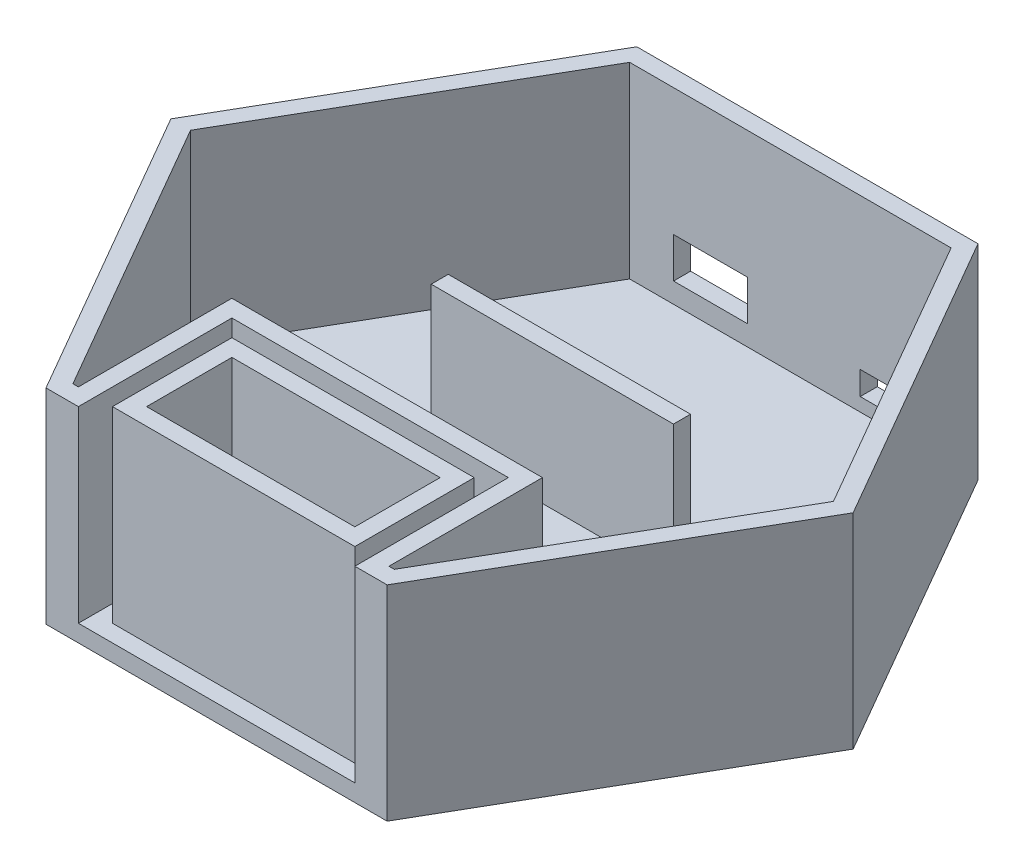
SolidWorks part; units mm, degrees
ref_plane "Front Plane" through (0, 0, 0) normal (0, 0, 1) x (1, 0, 0)
ref_plane "Top Plane" through (0, 0, 0) normal (0, 1, 0) x (1, 0, 0)
ref_plane "Right Plane" through (0, 0, 0) normal (1, 0, 0) x (0, 0, -1)
sketch "Sketch2" plane through (0, 0, 0) normal (0, 1, 0) x (1, 0, 0)
  line L0 (0, 0) -> (153.0899, 0) construction
  line L1 (76.2, 0) -> (101.6, 43.9941)
  line L2 (101.6, 43.9941) -> (76.2, 87.9882)
  line L3 (76.2, 87.9882) -> (25.4, 87.9882)
  line L4 (25.4, 87.9882) -> (0, 43.9941)
  line L5 (0, 43.9941) -> (25.4, 0)
  line L6 (25.4, 0) -> (76.2, 0)
  line L7 (0, 0) -> (0, 103.6086) construction
  circle A0 centre (50.8, 43.9941) radius 43.9941 construction
  dimension "D1" = 50.8
extrude "Boss-Extrude1" add sketch "Sketch2" along normal blind 2.54
sketch "Sketch3" plane through (0, 0, 0) normal (0, 1, 0) x (1, 0, 0)
  line L0 (25.4, 87.9882) -> (0, 43.9941)
  line L1 (0, 43.9941) -> (25.4, 0)
  line L3 (76.2, 0) -> (101.6, 43.9941)
  line L4 (101.6, 43.9941) -> (76.2, 87.9882)
  line L5 (76.2, 87.9882) -> (25.4, 87.9882)
  line L6 (26.8665, 85.4482) -> (2.9329, 43.9941)
  line L7 (2.9329, 43.9941) -> (26.8665, 2.54)
  line L9 (74.7335, 2.54) -> (98.6671, 43.9941)
  line L10 (98.6671, 43.9941) -> (74.7335, 85.4482)
  line L11 (74.7335, 85.4482) -> (26.8665, 85.4482)
  line L14 (30.2211, 22.86) -> (71.3908, 22.86)
  line L22 (32.7611, 20.32) -> (32.7611, 2.54)
  line L23 (32.7611, 2.54) -> (32.7611, 20.32)
  line L24 (68.8508, 20.32) -> (68.8508, 2.54)
  line L25 (32.7611, 2.54) -> (68.8508, 2.54)
  line L27 (35.3011, 17.78) -> (66.3108, 17.78)
  line L28 (35.3011, 17.78) -> (35.3011, 5.08)
  line L29 (35.3011, 5.08) -> (66.3108, 5.08)
  line L30 (32.7611, 20.32) -> (68.8508, 20.32)
  line L31 (26.8665, 2.54) -> (27.6811, 2.54)
  line L32 (27.6811, 2.54) -> (27.6811, 25.4)
  line L33 (27.6811, 25.4) -> (73.9308, 25.4)
  line L36 (25.4, 0) -> (76.2, 0) construction
  line L37 (30.2211, 0) -> (25.4, 0)
  line L39 (71.3908, 0) -> (76.2, 0)
  line L40 (71.3908, 22.86) -> (71.3908, 0)
  line L41 (30.2211, 22.86) -> (30.2211, 0)
  line L42 (73.9308, 25.4) -> (73.9308, 2.54)
  line L43 (73.9308, 2.54) -> (74.7335, 2.54)
  line L44 (66.3108, 17.78) -> (66.3108, 5.08)
  dimension "D1" = 2.54
  dimension "D2" = 2.54
  dimension "D3" = 2.54
  dimension "D4" = 2.54
  dimension "D5" = 2.54
  dimension "D6" = 2.54
  dimension "D7" = 2.54
  dimension "D8" = 2.54
  dimension "D9" = 2.54
  dimension "D10" = 2.54
  dimension "D11" = 2.54
  dimension "D12" = 2.54
  dimension "D13" = 2.54
  dimension "D14" = 2.54
  dimension "D15" = 2.54
  dimension "D16" = 25.4
  dimension "D17" = 2.54
extrude "Boss-Extrude2" add sketch "Sketch3" along normal blind 30.48 contours L30 L22 L25 L24 L27 L44 L29 L28 | L41 L14 L40 L39 L3 L4 L5 L0 L1 L37 L43 L42 L33 L32 L31 L7 L6 L11 L10 L9
sketch "Sketch5" plane through (0, 2.54, 0) normal (0, 1, 0) x (1, 0, 0)
  line L0 (30.2211, 0) -> (25.4, 0) construction
  line L3 (32.7611, 20.32) -> (32.7611, 2.54) construction
  line L4 (68.8389, 52.54) -> (32.7611, 52.54)
  line L5 (68.8389, 52.54) -> (68.8389, 50)
  line L6 (68.8389, 50) -> (32.7611, 50)
  line L7 (32.7611, 52.54) -> (32.7611, 50)
  line L8 (68.8389, 52.54) -> (32.7611, 50) construction
  line L9 (68.8389, 50) -> (32.7611, 52.54) construction
  point P7 (50.8, 51.27)
  dimension "D1" = 2.54
  dimension "D2" = 50
extrude "Boss-Extrude3" add sketch "Sketch5" along normal blind 20
sketch "Sketch7" plane through (0, 0, -85.4482) normal (0, 0, 1) x (1, 0, 0)
  line L0 (76.2, 30.48) -> (76.2, 0) construction
  line L1 (70.2, 8.04) -> (61.2, 8.04)
  line L2 (70.2, 8.04) -> (70.2, 4.54)
  line L3 (70.2, 4.54) -> (61.2, 4.54)
  line L4 (61.2, 8.04) -> (61.2, 4.54)
  line L5 (33.4, 11.54) -> (44.4, 11.54)
  line L6 (33.4, 11.54) -> (33.4, 5.54)
  line L7 (33.4, 5.54) -> (44.4, 5.54)
  line L8 (44.4, 11.54) -> (44.4, 5.54)
  line L9 (68.8508, 2.54) -> (32.7611, 2.54) construction
  line L10 (25.4, 30.48) -> (25.4, 0) construction
  dimension "D1" = 6
  dimension "D2" = 9
  dimension "D3" = 3.5
  dimension "D4" = 2
  dimension "D5" = 8
  dimension "D6" = 11
  dimension "D7" = 3
  dimension "D8" = 6
extrude "Cut-Extrude1" cut sketch "Sketch7" against normal through all
